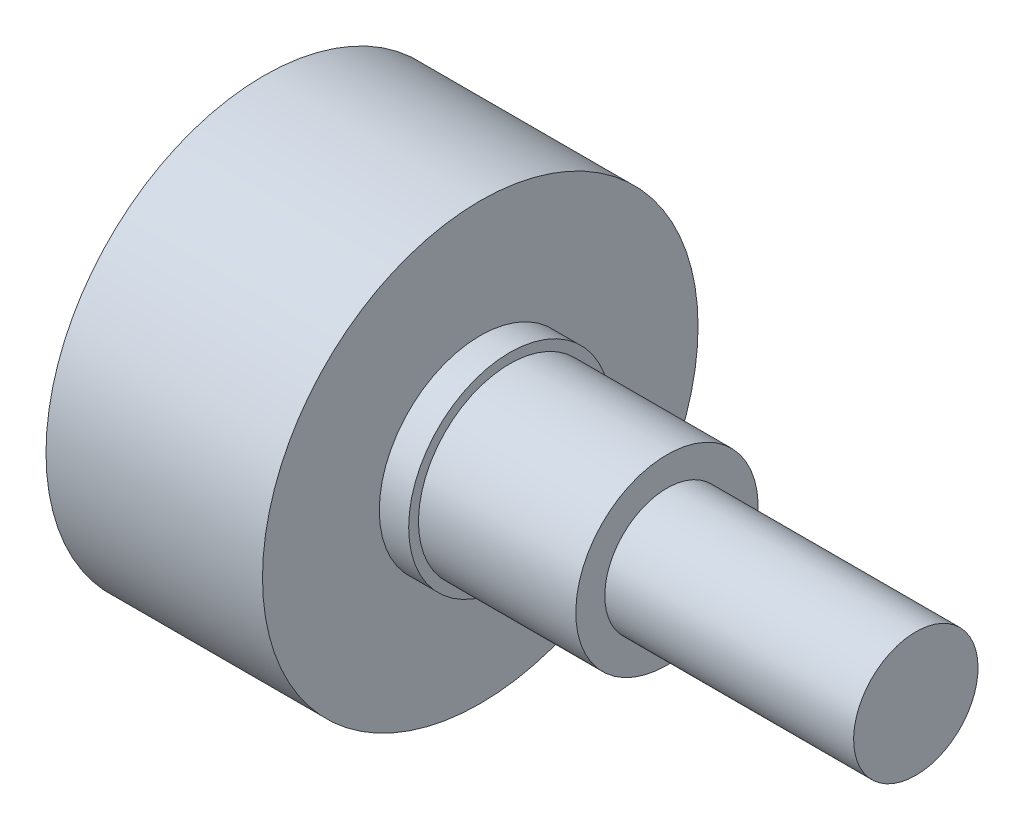
SolidWorks part; units mm, degrees
ref_plane "Front Plane" through (0, 0, 0) normal (0, 0, 1) x (1, 0, 0)
ref_plane "Top Plane" through (0, 0, 0) normal (0, 1, 0) x (1, 0, 0)
ref_plane "Right Plane" through (0, 0, 0) normal (1, 0, 0) x (0, 0, -1)
sketch "Sketch1" plane through (0, 0, 0) normal (0, 0, 1) x (1, 0, 0)
  line L0 (-16.64, 0) -> (16.64, 0)
  line L1 (16.64, 0) -> (16.64, 3.175)
  line L2 (16.64, 3.175) -> (3.94, 3.175)
  line L3 (3.94, 3.175) -> (3.94, 4.655)
  line L4 (3.94, 4.655) -> (-4.09, 4.655)
  line L6 (-5.59, 11.115) -> (-16.64, 11.115)
  line L7 (-16.64, 11.115) -> (-16.64, 0)
  line L8 (-5.59, 11.115) -> (-5.59, 5.155)
  line L9 (-5.59, 5.155) -> (-4.09, 5.155)
  line L10 (-4.09, 5.155) -> (-4.09, 4.655)
  point P3 (0, 0)
  dimension "D1" = 3.175
  dimension "D2" = 5.155
  dimension "D3" = 11.115
  dimension "D4" = 1.5
  dimension "D5" = 11.05
  dimension "D6" = 9.53
  dimension "D7" = 22.23
  dimension "D8" = 0.5
revolve "Revolve1" add sketch "Sketch1" angle 360 about L0
sketch "Sketch2" plane through (-16.64, 0, 0) normal (-1, 0, 0) x (0, 0, 1)
  circle A0 centre (0, 0) radius 5.525 construction
  circle A1 centre (-3.905, 3.9085) radius 1
  circle A2 centre (3.905, 3.9085) radius 1
  circle A3 centre (0, -5.525) radius 1
  dimension "D1" = 11.05
  dimension "D2" = 7.81
  dimension "D3" = 2
extrude "Boss-Extrude1" add sketch "Sketch2" along normal offset from surface (2.49 mm away) 13.54 up to face at (-5.59, -11.115, 0)
